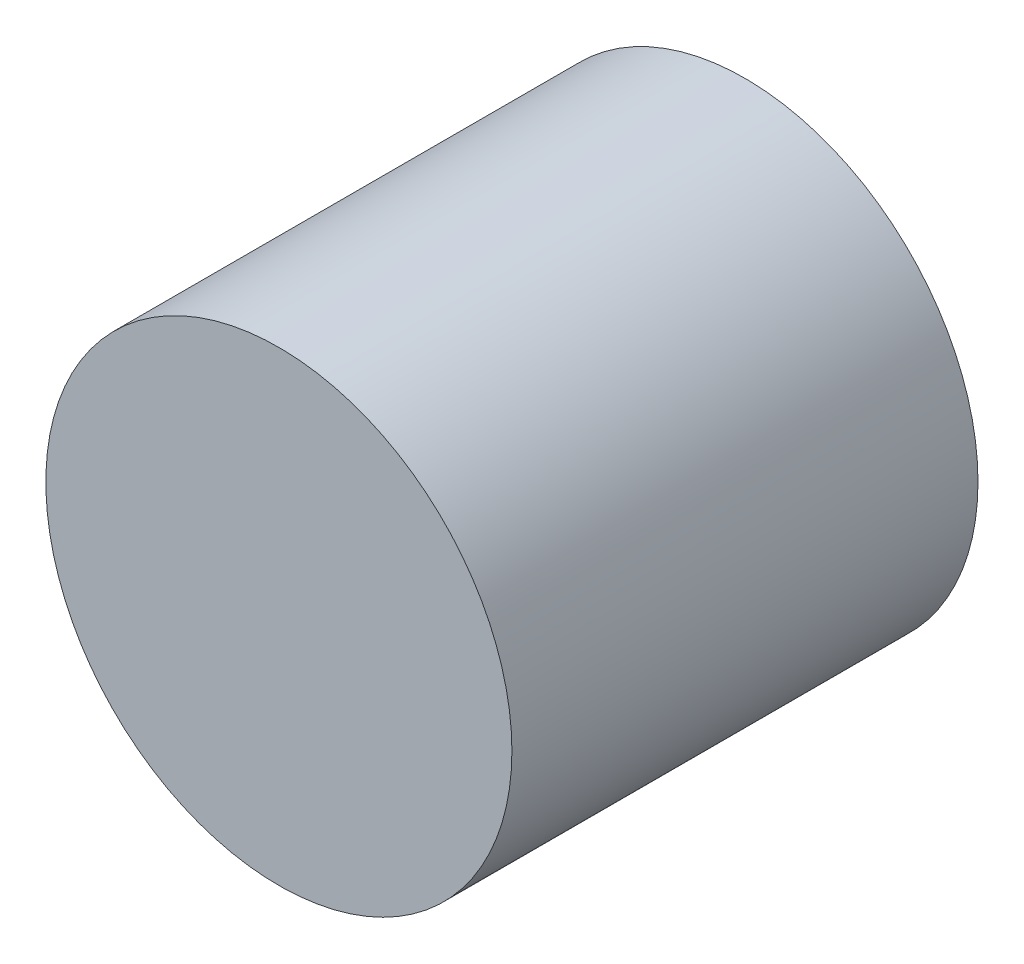
SolidWorks part; units mm, degrees
ref_plane "Front Plane" through (0, 0, 0) normal (0, 0, 1) x (1, 0, 0)
ref_plane "Top Plane" through (0, 0, 0) normal (0, 1, 0) x (1, 0, 0)
ref_plane "Right Plane" through (0, 0, 0) normal (1, 0, 0) x (0, 0, -1)
sketch "Sketch1" plane through (0, 0, 0) normal (0, 0, 1) x (1, 0, 0)
  circle A0 centre (0, 0) radius 25.4
  dimension "D1" = 50.8
extrude "Boss-Extrude1" add sketch "Sketch1" along normal blind 50.8
